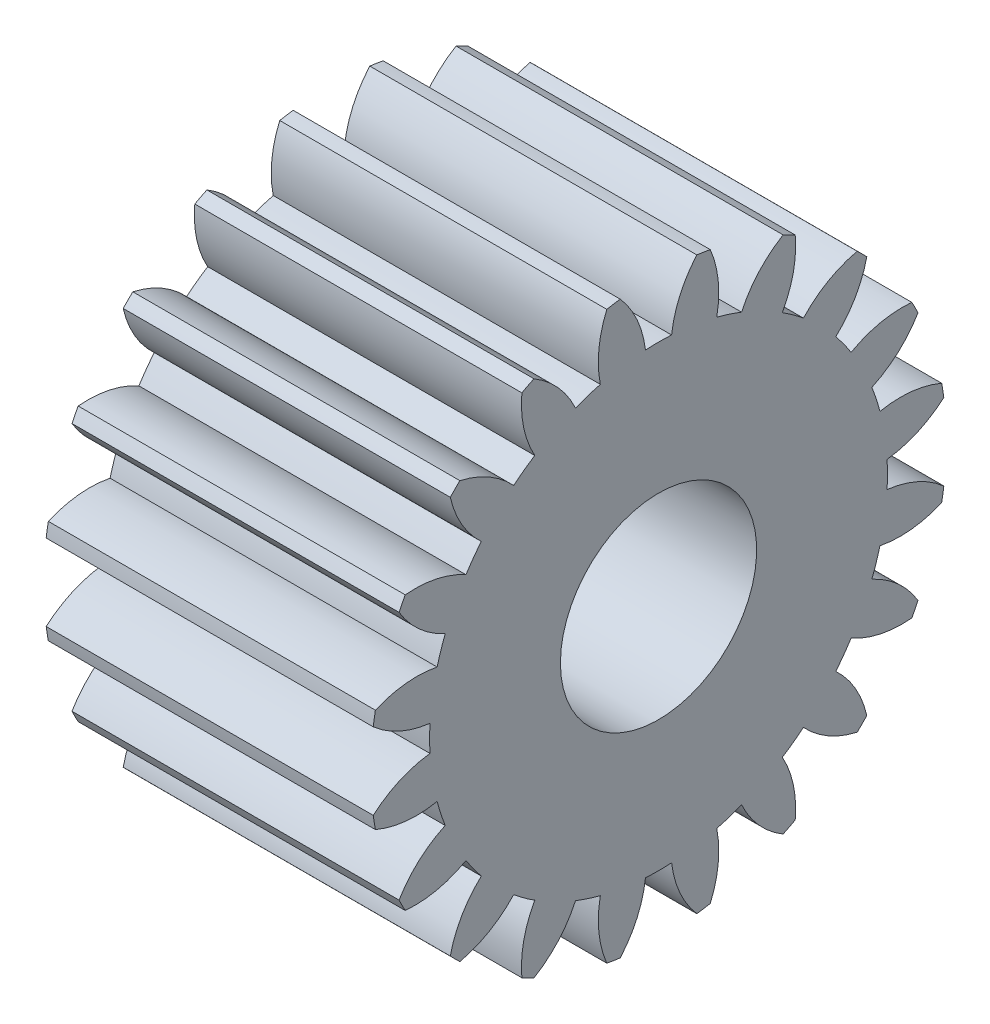
SolidWorks part; units mm, degrees
ref_plane "Plane1" through (0, 0, 0) normal (0, 0, 1) x (1, 0, 0)
ref_plane "Plane2" through (0, 0, 0) normal (0, 1, 0) x (1, 0, 0)
ref_plane "Plane3" through (0, 0, 0) normal (1, 0, 0) x (0, 0, -1)
sketch "HoldingSke" plane through (0, 0, 0) normal (0, 1, 0) x (1, 0, 0)
  line L0 (0, 0) -> (1.1746, -0.4275)
  line L1 (-15, 0) -> (100, 0) construction
  line L2 (0, 0) -> (-2.1039, 2.3779)
  line L3 (0, 0) -> (-11.863, 4.5341)
  line L4 (0, 0) -> (8.1152, 2.9537)
  line L5 (0, 0) -> (-46.8476, -17.4728)
  line L6 (0, 0) -> (-8.2896, -5.593)
  line L7 (-2.1039, 2.3779) -> (8.6586, 51.2059)
  line L8 (-76.2, 54.61) -> (-75.2, 54.61)
  line L9 (-71.009, 38.7566) -> (-53.1078, 45.2721)
  line L10 (-76.2, 71.12) -> (104.1128, 71.12)
  line L11 (0, 0) -> (-10, 0)
  line L12 (-76.2, 101.6) -> (-76.17, 101.6)
  line L13 (24.9733, 27.94) -> (52.9518, 28.4284)
  line L14 (24.9733, 27.94) -> (24.9743, 27.94)
  line L15 (24.9733, 27.94) -> (100.4006, 29.5858)
  line L16 (-63.627, -0.8) -> (-12.827, -0.8)
  circle A0 centre (0, 0) radius 3
  circle A1 centre (0, 0) radius 6.999
  circle A2 centre (0, 0) radius 37.5
  circle A3 centre (0, 0) radius 3
  dimension "MHD" = 13.998
  dimension "Hub_dia" = 75
  dimension "Bore" = 6
  dimension "MBD" = 6
  dimension "Num_teeth" = 20
  dimension "Pitch" = 1.25
  dimension "Overall_len" = 50
  dimension "Show_teeth" = 20
  dimension "Thickness" = 10
  dimension "OAL" = 50.0001
  dimension "T_dim" = 1
  dimension "Ap" = 20
  dimension "H" = 19.05
  dimension "Pitch_radius" = 180.3128
  dimension "Width" = 10
  dimension "Backlash" = 0.03
  dimension "Addendum_fac" = 1
  dimension "Dedendum_fac" = 1.25
  dimension "Clearance_fac" = 0.25
  dimension "Dedendum_add" = 0.001
  dimension "Module" = 0.8
sketch "BasProSke" plane through (0, 0, 0) normal (0, 1, 0) x (1, 0, 0)
  line L0 (-10, 0) -> (60, 0) construction
  line L1 (0, 0) -> (0, 8.8)
  line L2 (0, 0) -> (10, 0)
  line L3 (10, 0) -> (10, 8.8)
  line L4 (10, 8.8) -> (0, 8.8)
  dimension "Thickness" = 10
  dimension "Diameter" = 17.6
revolve "Base-Revolve" add sketch "BasProSke" angle 360 about L0
sketch "TooCutSke" plane through (0, 0, 0) normal (1, 0, 0) x (0, 0, -1)
  line L1 (0, 0) -> (0, 107) construction
  line L2 (0, 0) -> (-0.6801, 7.971) construction
  line L3 (0, 0) -> (-2.4965, 15.7621) construction
  line L4 (-0.6801, 7.971) -> (-1.2482, 7.8811) construction
  arc A0 (0.3993, 6.9876) -> (-0.3993, 6.9876) centre (0, 0) ccw
  arc A1 (1.1915, 8.7446) -> (-1.1915, 8.7446) centre (0, 0) ccw
  circle A2 centre (0, 0) radius 8 construction
  circle A3 centre (0, 0) radius 7.5175 construction
  arc A4 (-0.3993, 6.9876) -> (-1.1915, 8.7446) centre (-3.5772, 6.6119) ccw
  arc A5 (1.1915, 8.7446) -> (0.3993, 6.9876) centre (3.5772, 6.6119) ccw
  dimension "Root_dia" = 13.998
  dimension "Overcut_dia" = 17.6508
  dimension "Pitch_dia" = 16
  dimension "Base_dia" = 15.0351
  dimension "Flank_rad" = 3.2
  dimension "Half_ang" = 9
  dimension "Half_CT" = 0.5752
extrude "ToothCut" cut sketch "TooCutSke" along normal through all
fillet "Breaks" [suppressed] radius 0.016
fillet "RootFillets" [suppressed] radius 0.201
pattern_circular "TeethCuts" count 20 every 18 about axis through (-10, 0, 0) along (1, 0, 0) of "ToothCut", "RootFillets", "Breaks"
sketch "HubNeaOneSke" plane through (0, 0, 0) normal (-1, 0, 0) x (0, 0, 1)
  circle A0 centre (0, 0) radius 6.999
  dimension "Diameter" = 13.998
extrude "HubNearOne" [suppressed] add sketch "HubNeaOneSke" along normal blind 40.0001
sketch "HubNeaBotSke" plane through (0, 0, 0) normal (-1, 0, 0) x (0, 0, 1)
  circle A0 centre (0, 0) radius 6.999
  dimension "Diameter" = 13.998
extrude "HubNearBoth" [suppressed] add sketch "HubNeaBotSke" along normal blind 20
ref_plane "FarPln" through (10, 0, 0) normal (1, 0, 0) x (0, 0, -1)
sketch "HubFarSke" plane through (10, 0, 0) normal (1, 0, 0) x (0, 0, -1)
  circle A0 centre (0, 0) radius 6.999
  dimension "Diameter" = 13.998
extrude "HubFar" [suppressed] add sketch "HubFarSke" along normal blind 20
sketch "BorSke" plane through (0, 0, 0) normal (1, 0, 0) x (0, 0, -1)
  circle A0 centre (0, 0) radius 3
  dimension "Diameter" = 6
extrude "Bore" cut sketch "BorSke" along normal mid plane 100.0001
sketch "KeySke" plane through (0, 0, 0) normal (1, 0, 0) x (0, 0, -1)
  line L0 (-1, 0) -> (-1, 4)
  line L1 (-1, 4) -> (1, 4)
  line L2 (1, 4) -> (1, 0)
  line L3 (0, 0) -> (0, 34) construction
  line L4 (-1, 0) -> (1, 0)
  dimension "Offset" = 4
  dimension "Width" = 2
extrude "Keyway" [suppressed] cut sketch "KeySke" along normal mid plane 100.0001
pattern_circular "Keyway2" [suppressed] count 2 every 90 about axis through (-10, 0, 0) along (1, 0, 0)
equation "' \"Module@HoldingSke\" = 6.35"
equation "' \"Num_teeth@HoldingSke\" = 12"
equation "' \"Ap@HoldingSke\" =  20"
equation "' \"Ap@HoldingSke\" = 20"
equation "' \"Width@HoldingSke\" = 0.5 * 25.4"
equation "' \"Hub_dia@HoldingSke\"= 1 * 25.4"
equation "' \"Hub_dia@HoldingSke\" = 1 * 25.4"
equation "' \"Overall_len@HoldingSke\" = 1.0 * 25.4"
equation "' \"Bore@HoldingSke\" = 0.75 * 25.4"
equation "' \"T_dim@HoldingSke\" = 0.1 * 25.4"
equation "' \"Width@KeySke\" = 0.25 * 25.4"
equation "' \"Show_teeth@HoldingSke\" = 13"
equation "' \"Backlash@HoldingSke\" = 0.009 * 25.4"
equation "' \"Addendum_fac@HoldingSke\" = 1.0"
equation "' \"Dedendum_fac@HoldingSke\" = 1.25"
equation "' \"Dedendum_add@HoldingSke\" = 0.00005 * 25.4"
equation "' \"Clearance_fac@HoldingSke\" = 0.25"
equation "\"Pitch@HoldingSke\" = 1 / \"Module@HoldingSke\""
equation "\"Overcut_dia@TooCutSke\" = (\"Num_teeth@HoldingSke\" + 2 * \"Addendum_fac@HoldingSke\") / \"Pitch@HoldingSke\" + 0.002 * 25.4"
equation "\"Pitch_dia@TooCutSke\" = \"Num_teeth@HoldingSke\" / \"Pitch@HoldingSke\""
equation "\"Base_dia@TooCutSke\" = \"Num_teeth@HoldingSke\" / \"Pitch@HoldingSke\" * cos((\"Ap@HoldingSke\"  * 3.14159265 / 180))"
equation "\"Root_dia@TooCutSke\" = (\"Num_teeth@HoldingSke\" + 2) / \"Pitch@HoldingSke\" - 2 * (\"Addendum_fac@HoldingSke\" + \"Dedendum_fac@HoldingSke\") / \"Pitch@HoldingSke\" - \"Dedendum_add@HoldingSke\" * 2"
equation "\"Half_ang@TooCutSke\" = 180 / \"Num_teeth@HoldingSke\""
equation "\"Half_CT@TooCutSke\" = \"Num_teeth@HoldingSke\" / \"Pitch@HoldingSke\" * sin((3.14159265 / 2 / \"Num_teeth@HoldingSke\")) / 2 - 7 * \"Backlash@HoldingSke\" / 4"
equation "\"Flank_rad@TooCutSke\" = \"Num_teeth@HoldingSke\" / \"Pitch@HoldingSke\" / 5"
equation "\"Radius@RootFillets\" = \"Clearance_fac@HoldingSke\" / \"Pitch@HoldingSke\" + \"Dedendum_add@HoldingSke\""
equation "\"Break_rad@Breaks\" = 0.02 / \"Pitch@HoldingSke\""
equation "\"Thickness@HoldingSke\" = \"Width@HoldingSke\""
equation "\"OAL@HoldingSke\" = \"Thickness@HoldingSke\""
equation "\"MHD@HoldingSke\" = (\"Num_teeth@HoldingSke\" + 2) / \"Pitch@HoldingSke\" - 2 * (\"Addendum_fac@HoldingSke\" + \"Dedendum_fac@HoldingSke\")  / \"Pitch@HoldingSke\" - \"Dedendum_add@HoldingSke\" * 2"
equation "\"MBD@HoldingSke\" = (\"Num_teeth@HoldingSke\" + 2) / \"Pitch@HoldingSke\" - 2 * (\"Addendum_fac@HoldingSke\" + \"Dedendum_fac@HoldingSke\")  / \"Pitch@HoldingSke\" - \"Dedendum_add@HoldingSke\" * 2 - 0.002 * 25.4"
equation "\"MHD@HoldingSke\" = ((sgn( \"MHD@HoldingSke\" - \"Hub_dia@HoldingSke\" )-1)*( \"MHD@HoldingSke\" - \"Hub_dia@HoldingSke\" ))/-2+ \"Hub_dia@HoldingSke\""
equation "\"MBD@HoldingSke\" = ((sgn( \"MBD@HoldingSke\" - \"Bore@HoldingSke\" )-1)*( \"MBD@HoldingSke\" - \"Bore@HoldingSke\" ))/-2+ \"Bore@HoldingSke\""
equation "\"OAL@HoldingSke\" = ((sgn( \"OAL@HoldingSke\" - \"Overall_len@HoldingSke\" )+1)*( \"OAL@HoldingSke\" - \"Overall_len@HoldingSke\" ))/2 + \"Overall_len@HoldingSke\" + 0.000002 * 25.4"
equation "\"Num_teeth@TeethCuts\" = int( \"Show_teeth@HoldingSke\" ) + 1"
equation "\"Num_teeth@TeethCuts\" = ((sgn( \"Num_teeth@TeethCuts\" - \"Num_teeth@HoldingSke\" )-1)*( \"Num_teeth@TeethCuts\" - \"Num_teeth@HoldingSke\" ))/-2+ \"Num_teeth@HoldingSke\""
equation "\"Num_teeth@TeethCuts\" = ((sgn( \"Num_teeth@TeethCuts\" - 2.0)+1)*( \"Num_teeth@TeethCuts\" - 2.0))/2 +2.0"
equation "\"Angle@TeethCuts\" = 360.0 / \"Num_teeth@HoldingSke\""
equation "\"Diameter@BasProSke\" = (\"Num_teeth@HoldingSke\" + 2 * \"Addendum_fac@HoldingSke\") / \"Pitch@HoldingSke\""
equation "\"Thickness@BasProSke\"  = \"Thickness@HoldingSke\""
equation "' \"Fillet_rad@BasProSke\" =  \"Thickness@HoldingSke\" * 0.05"
equation "' \"Fillet_rad@BasProSke\" = \"Thickness@HoldingSke\" * 0.05"
equation "\"MHD@HoldingSke\" = ((sgn( \"MHD@HoldingSke\" - \"Root_dia@TooCutSke\" )-1)*( \"MHD@HoldingSke\" - \"Root_dia@TooCutSke\" ))/-2+ \"Root_dia@TooCutSke\""
equation "\"Diameter@HubNeaOneSke\" = \"MHD@HoldingSke\""
equation "\"Length@HubNearOne\" = \"OAL@HoldingSke\" - \"Thickness@BasProSke\""
equation "\"Diameter@HubNeaBotSke\" = \"MHD@HoldingSke\""
equation "\"Length@HubNearBoth\" = ( \"OAL@HoldingSke\" - \"Thickness@BasProSke\" ) / 2.0"
equation "\"Thickness@FarPln\" = \"Thickness@BasProSke\""
equation "\"Diameter@HubFarSke\" = \"MHD@HoldingSke\""
equation "\"Length@HubFar\" = ( \"OAL@HoldingSke\" - \"Thickness@BasProSke\" ) / 2.0"
equation "\"Diameter@BorSke\" = \"MBD@HoldingSke\""
equation "\"D1@Bore\" = \"OAL@HoldingSke\" * 2.0"
equation "\"D1@Keyway\" = \"OAL@HoldingSke\" * 2.0"
equation "\"Offset@KeySke\" = \"T_dim@HoldingSke\" + \"MBD@HoldingSke\" / 2.0"
